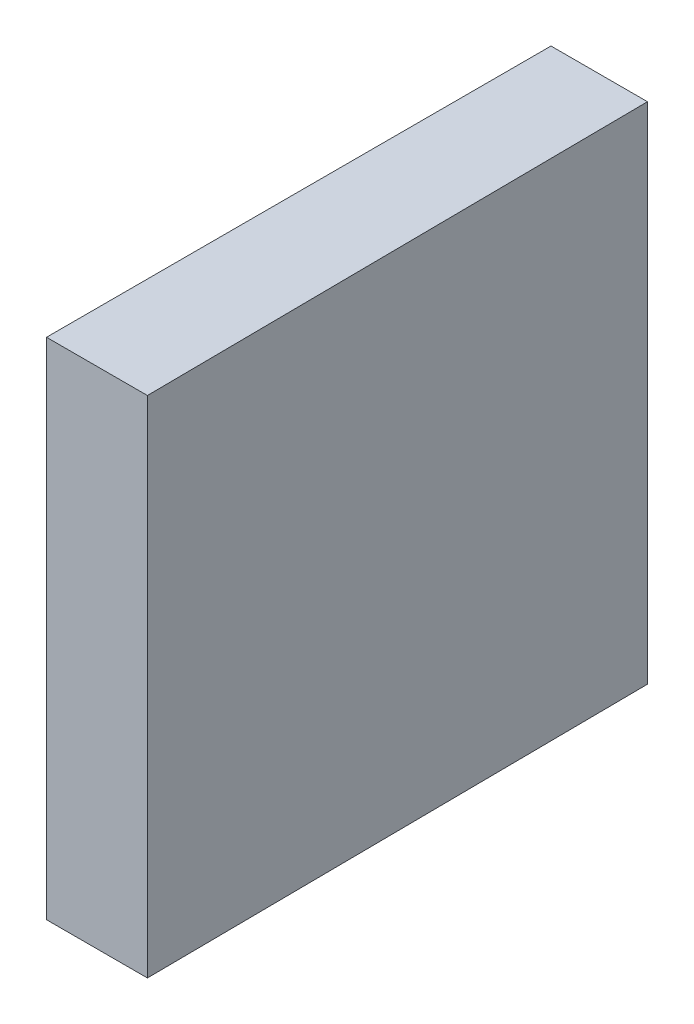
SolidWorks part; units mm, degrees
ref_plane "前视基准面" through (0, 0, 0) normal (0, 0, 1) x (1, 0, 0)
ref_plane "上视基准面" through (0, 0, 0) normal (0, 1, 0) x (1, 0, 0)
ref_plane "右视基准面" through (0, 0, 0) normal (1, 0, 0) x (0, 0, -1)
sketch "草图1" plane through (0, 0, 0) normal (0, 1, 0) x (1, 0, 0)
  line L0 (-12.1202, 0) -> (19.0875, 0) construction
  line L1 (0, 12.5) -> (0, -12.5)
  line L2 (0, -12.5) -> (5, -12.5)
  line L3 (5, -12.5) -> (4.7818, 12.5)
  line L4 (0, 12.5) -> (4.7818, 12.5)
  point P5 (0, 0)
  dimension "D1" = 5
  dimension "D2" = 25
  dimension "D3" = 0.5
extrude "凸台-拉伸1" add sketch "草图1" along normal blind 25
